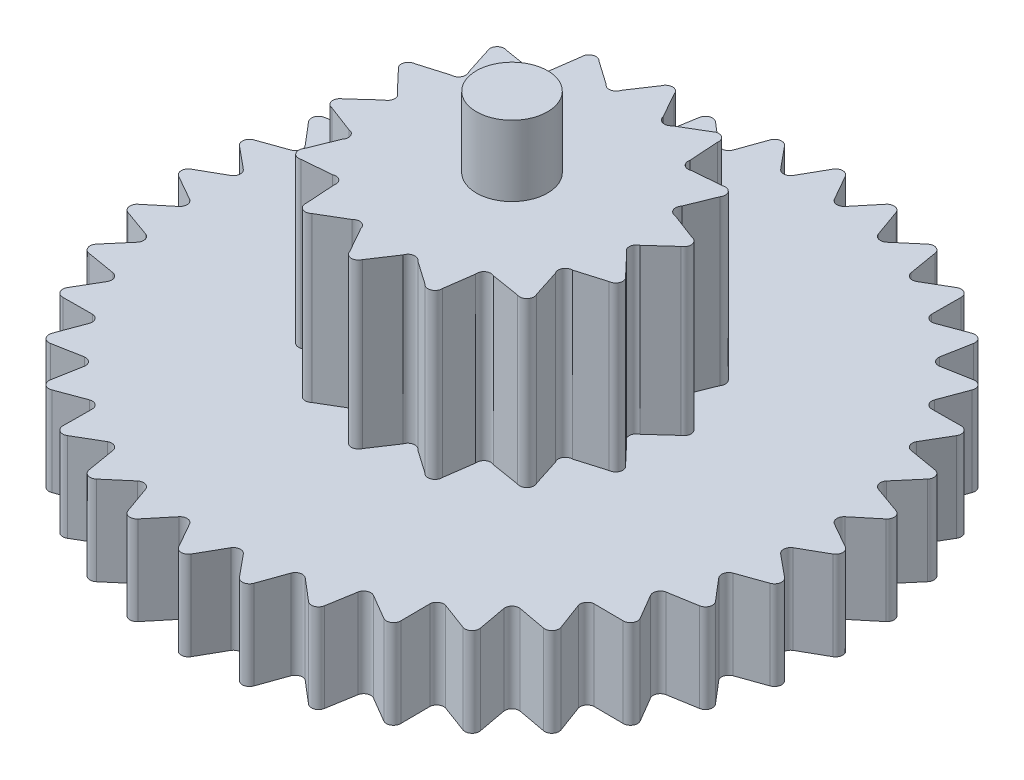
SolidWorks part; units mm, degrees
material "ABS"
ref_plane "Front Plane" through (0, 0, 0) normal (0, 0, 1) x (1, 0, 0)
ref_plane "Top Plane" through (0, 0, 0) normal (0, 1, 0) x (1, 0, 0)
ref_plane "Right Plane" through (0, 0, 0) normal (1, 0, 0) x (0, 0, -1)
sketch "Sketch1" plane through (0, 0, 0) normal (0, 1, 0) x (1, 0, 0)
  line L0 (-8.2272, 4.75) -> (-8.9271, 3.2492) construction
  line L1 (0, 9.5) -> (-1.6497, 9.3557) construction
  line L2 (-1.6497, 9.3557) -> (-3.2492, 8.9271) construction
  line L3 (-3.2492, 8.9271) -> (-4.75, 8.2272) construction
  line L4 (-4.75, 8.2272) -> (-6.1065, 7.2774) construction
  line L5 (-6.1065, 7.2774) -> (-7.2774, 6.1065) construction
  line L6 (-7.2774, 6.1065) -> (-8.2272, 4.75) construction
  line L7 (-8.9271, 3.2492) -> (-9.3557, 1.6497) construction
  line L8 (-9.3557, 1.6497) -> (-9.5, 0) construction
  line L9 (-9.5, 0) -> (-9.3557, -1.6497) construction
  line L10 (-9.3557, -1.6497) -> (-8.9271, -3.2492) construction
  line L11 (-8.9271, -3.2492) -> (-8.2272, -4.75) construction
  line L12 (-8.2272, -4.75) -> (-7.2774, -6.1065) construction
  line L13 (-7.2774, -6.1065) -> (-6.1065, -7.2774) construction
  line L14 (-6.1065, -7.2774) -> (-4.75, -8.2272) construction
  line L15 (-4.75, -8.2272) -> (-3.2492, -8.9271) construction
  line L16 (-3.2492, -8.9271) -> (-1.6497, -9.3557) construction
  line L17 (-1.6497, -9.3557) -> (0, -9.5) construction
  line L18 (0, -9.5) -> (1.6497, -9.3557) construction
  line L19 (1.6497, -9.3557) -> (3.2492, -8.9271) construction
  line L20 (3.2492, -8.9271) -> (4.75, -8.2272) construction
  line L21 (4.75, -8.2272) -> (6.1065, -7.2774) construction
  line L22 (6.1065, -7.2774) -> (7.2774, -6.1065) construction
  line L23 (7.2774, -6.1065) -> (8.2272, -4.75) construction
  line L24 (8.2272, -4.75) -> (8.9271, -3.2492) construction
  line L25 (8.9271, -3.2492) -> (9.3557, -1.6497) construction
  line L26 (9.3557, -1.6497) -> (9.5, 0) construction
  line L27 (9.5, 0) -> (9.3557, 1.6497) construction
  line L28 (9.3557, 1.6497) -> (8.9271, 3.2492) construction
  line L29 (8.9271, 3.2492) -> (8.2272, 4.75) construction
  line L30 (8.2272, 4.75) -> (7.2774, 6.1065) construction
  line L31 (7.2774, 6.1065) -> (6.1065, 7.2774) construction
  line L32 (6.1065, 7.2774) -> (4.75, 8.2272) construction
  line L33 (4.75, 8.2272) -> (3.2492, 8.9271) construction
  line L34 (3.2492, 8.9271) -> (1.6497, 9.3557) construction
  line L35 (1.6497, 9.3557) -> (0, 9.5) construction
  line L36 (0, 9.5) -> (0, 9.2952) construction
  line L37 (0, 9.5) -> (-0.7202, 8.2324) construction
  line L38 (-0.8248, 9.4278) -> (-0.7202, 8.2324) construction
  line L39 (0, 9.5) -> (0.7202, 8.2324) construction
  line L40 (0.7202, 8.2324) -> (0.8248, 9.4278) construction
  line L41 (1.4237, 9.0826) -> (0.901, 8.4508)
  line L42 (0.1751, 9.1918) -> (0.5802, 8.4789)
  line L43 (-0.1751, 9.1918) -> (-0.5802, 8.4789)
  line L44 (1.7686, 9.0218) -> (2.0437, 8.2493)
  line L45 (2.9792, 8.6974) -> (2.3547, 8.166)
  line L46 (3.3083, 8.5776) -> (3.4452, 7.7691)
  line L47 (4.4443, 8.0479) -> (3.737, 7.633)
  line L48 (4.7476, 7.8728) -> (4.7419, 7.0528)
  line L49 (5.7743, 7.1539) -> (5.0057, 6.8681)
  line L50 (6.0425, 6.9288) -> (5.8946, 6.1223)
  line L51 (6.9288, 6.0425) -> (6.1223, 5.8946)
  line L52 (7.1539, 5.7743) -> (6.8681, 5.0057)
  line L53 (7.8728, 4.7476) -> (7.0528, 4.7419)
  line L54 (8.0479, 4.4443) -> (7.633, 3.737)
  line L55 (8.5776, 3.3083) -> (7.7691, 3.4452)
  line L56 (8.6974, 2.9792) -> (8.166, 2.3547)
  line L57 (9.0218, 1.7686) -> (8.2493, 2.0437)
  line L58 (9.0826, 1.4237) -> (8.4508, 0.901)
  line L59 (9.1918, 0.1751) -> (8.4789, 0.5802)
  line L60 (9.1918, -0.1751) -> (8.4789, -0.5802)
  line L61 (9.0826, -1.4237) -> (8.4508, -0.901)
  line L62 (9.0218, -1.7686) -> (8.2493, -2.0437)
  line L63 (8.6974, -2.9792) -> (8.166, -2.3547)
  line L64 (8.5776, -3.3083) -> (7.7691, -3.4452)
  line L65 (8.0479, -4.4443) -> (7.633, -3.737)
  line L66 (7.8728, -4.7476) -> (7.0528, -4.7419)
  line L67 (7.1539, -5.7743) -> (6.8681, -5.0057)
  line L68 (6.9288, -6.0425) -> (6.1223, -5.8946)
  line L69 (6.0425, -6.9288) -> (5.8946, -6.1223)
  line L70 (5.7743, -7.1539) -> (5.0057, -6.8681)
  line L71 (4.7476, -7.8728) -> (4.7419, -7.0528)
  line L72 (4.4443, -8.0479) -> (3.737, -7.633)
  line L73 (3.3083, -8.5776) -> (3.4452, -7.7691)
  line L74 (2.9792, -8.6974) -> (2.3547, -8.166)
  line L75 (1.7686, -9.0218) -> (2.0437, -8.2493)
  line L76 (1.4237, -9.0826) -> (0.901, -8.4508)
  line L77 (0.1751, -9.1918) -> (0.5802, -8.4789)
  line L78 (-0.1751, -9.1918) -> (-0.5802, -8.4789)
  line L79 (-1.4237, -9.0826) -> (-0.901, -8.4508)
  line L80 (-1.7686, -9.0218) -> (-2.0437, -8.2493)
  line L81 (-2.9792, -8.6974) -> (-2.3547, -8.166)
  line L82 (-3.3083, -8.5776) -> (-3.4452, -7.7691)
  line L83 (-4.4443, -8.0479) -> (-3.737, -7.633)
  line L84 (-4.7476, -7.8728) -> (-4.7419, -7.0528)
  line L85 (-5.7743, -7.1539) -> (-5.0057, -6.8681)
  line L86 (-6.0425, -6.9288) -> (-5.8946, -6.1223)
  line L87 (-6.9288, -6.0425) -> (-6.1223, -5.8946)
  line L88 (-7.1539, -5.7743) -> (-6.8681, -5.0057)
  line L89 (-7.8728, -4.7476) -> (-7.0528, -4.7419)
  line L90 (-8.0479, -4.4443) -> (-7.633, -3.737)
  line L91 (-8.5776, -3.3083) -> (-7.7691, -3.4452)
  line L92 (-8.6974, -2.9792) -> (-8.166, -2.3547)
  line L93 (-9.0218, -1.7686) -> (-8.2493, -2.0437)
  line L94 (-9.0826, -1.4237) -> (-8.4508, -0.901)
  line L95 (-9.1918, -0.1751) -> (-8.4789, -0.5802)
  line L96 (-9.1918, 0.1751) -> (-8.4789, 0.5802)
  line L97 (-9.0826, 1.4237) -> (-8.4508, 0.901)
  line L98 (-9.0218, 1.7686) -> (-8.2493, 2.0437)
  line L99 (-8.6974, 2.9792) -> (-8.166, 2.3547)
  line L100 (-8.5776, 3.3083) -> (-7.7691, 3.4452)
  line L101 (-8.0479, 4.4443) -> (-7.633, 3.737)
  line L102 (-7.8728, 4.7476) -> (-7.0528, 4.7419)
  line L103 (-7.1539, 5.7743) -> (-6.8681, 5.0057)
  line L104 (-6.9288, 6.0425) -> (-6.1223, 5.8946)
  line L105 (-6.0425, 6.9288) -> (-5.8946, 6.1223)
  line L106 (-5.7743, 7.1539) -> (-5.0057, 6.8681)
  line L107 (-4.7476, 7.8728) -> (-4.7419, 7.0528)
  line L108 (-4.4443, 8.0479) -> (-3.737, 7.633)
  line L109 (-3.3083, 8.5776) -> (-3.4452, 7.7691)
  line L110 (-2.9792, 8.6974) -> (-2.3547, 8.166)
  line L111 (-1.7686, 9.0218) -> (-2.0437, 8.2493)
  line L112 (-1.4237, 9.0826) -> (-0.901, 8.4508)
  line L113 (0, -9.2952) -> (0, -9.5) construction
  line L114 (0.3636, 4.1956) -> (0.766, 3.4811)
  line L115 (-0.0146, 4.2155) -> (-0.469, 3.5329)
  line L116 (2.1488, 3.6227) -> (2.2013, 2.8044)
  line L117 (1.8167, 3.8048) -> (1.1112, 3.387)
  line L118 (3.5087, 2.332) -> (3.201, 1.572)
  line L119 (3.2885, 2.6402) -> (2.4715, 2.5699)
  line L120 (4.174, 0.5791) -> (3.5669, 0.0279)
  line L121 (4.1092, 0.9523) -> (3.3426, 1.2434)
  line L122 (4.0127, -1.2888) -> (3.2266, -1.5221)
  line L123 (4.1163, -0.9245) -> (3.552, -0.3296)
  line L124 (3.057, -2.9018) -> (2.2475, -2.7709)
  line L125 (3.3084, -2.6185) -> (3.0581, -1.8377)
  line L126 (1.4961, -3.9404) -> (0.8236, -3.4712)
  line L127 (1.8455, -3.7943) -> (1.9587, -2.9821)
  line L128 (-0.3609, -4.1989) -> (-0.7633, -3.4844)
  line L129 (0.0173, -4.2188) -> (0.4717, -3.5362)
  line L130 (-2.1462, -3.6261) -> (-2.1986, -2.8077)
  line L131 (-1.814, -3.8081) -> (-1.1085, -3.3903)
  line L132 (-3.506, -2.3354) -> (-3.1983, -1.5753)
  line L133 (-3.2858, -2.6435) -> (-2.4688, -2.5732)
  line L134 (-4.1713, -0.5824) -> (-3.5642, -0.0312)
  line L135 (-4.1065, -0.9557) -> (-3.3399, -1.2468)
  line L136 (-4.01, 1.2855) -> (-3.2239, 1.5187)
  line L137 (-4.1136, 0.9212) -> (-3.5493, 0.3263)
  line L138 (-3.0543, 2.8985) -> (-2.2448, 2.7676)
  line L139 (-3.3057, 2.6152) -> (-3.0554, 1.8344)
  line L140 (-1.4934, 3.9371) -> (-0.8209, 3.4679)
  line L141 (-1.8428, 3.7909) -> (-1.956, 2.9788)
  circle A0 centre (0, 0) radius 9.5 construction
  arc A1 (-0.1751, 9.1918) -> (0.1751, 9.1918) centre (0, 9.0952) cw
  arc A2 (0.5802, 8.4789) -> (0.7335, 8.3838) centre (0.7509, 8.5831) ccw
  arc A3 (-0.5802, 8.4789) -> (-0.7335, 8.3838) centre (-0.7509, 8.5831) cw
  arc A4 (0.901, 8.4508) -> (0.7335, 8.3838) centre (0.7509, 8.5831) cw
  arc A5 (1.4237, 9.0826) -> (1.7686, 9.0218) centre (1.5794, 8.957) cw
  arc A6 (2.0437, 8.2493) -> (2.1782, 8.1291) centre (2.2299, 8.3223) ccw
  arc A7 (2.3547, 8.166) -> (2.1782, 8.1291) centre (2.2299, 8.3223) cw
  arc A8 (2.9792, 8.6974) -> (3.3083, 8.5776) centre (3.1107, 8.5467) cw
  arc A9 (3.4452, 7.7691) -> (3.5567, 7.6273) centre (3.6412, 7.8086) ccw
  arc A10 (3.737, 7.633) -> (3.5567, 7.6273) centre (3.6412, 7.8086) cw
  arc A11 (4.4443, 8.0479) -> (4.7476, 7.8728) centre (4.5476, 7.8767) cw
  arc A12 (4.7419, 7.0528) -> (4.8271, 6.8939) centre (4.9418, 7.0577) ccw
  arc A13 (5.0057, 6.8681) -> (4.8271, 6.8939) centre (4.9418, 7.0577) cw
  arc A14 (5.7743, 7.1539) -> (6.0425, 6.9288) centre (5.8463, 6.9673) cw
  arc A15 (5.8946, 6.1223) -> (5.9509, 5.9509) centre (6.0923, 6.0923) ccw
  arc A16 (6.1223, 5.8946) -> (5.9509, 5.9509) centre (6.0923, 6.0923) cw
  arc A17 (6.9288, 6.0425) -> (7.1539, 5.7743) centre (6.9673, 5.8463) cw
  arc A18 (6.8681, 5.0057) -> (6.8939, 4.8271) centre (7.0577, 4.9418) ccw
  arc A19 (7.0528, 4.7419) -> (6.8939, 4.8271) centre (7.0577, 4.9418) cw
  arc A20 (7.8728, 4.7476) -> (8.0479, 4.4443) centre (7.8767, 4.5476) cw
  arc A21 (7.633, 3.737) -> (7.6273, 3.5567) centre (7.8086, 3.6412) ccw
  arc A22 (7.7691, 3.4452) -> (7.6273, 3.5567) centre (7.8086, 3.6412) cw
  arc A23 (8.5776, 3.3083) -> (8.6974, 2.9792) centre (8.5467, 3.1107) cw
  arc A24 (8.166, 2.3547) -> (8.1291, 2.1782) centre (8.3223, 2.2299) ccw
  arc A25 (8.2493, 2.0437) -> (8.1291, 2.1782) centre (8.3223, 2.2299) cw
  arc A26 (9.0218, 1.7686) -> (9.0826, 1.4237) centre (8.957, 1.5794) cw
  arc A27 (8.4508, 0.901) -> (8.3838, 0.7335) centre (8.5831, 0.7509) ccw
  arc A28 (8.4789, 0.5802) -> (8.3838, 0.7335) centre (8.5831, 0.7509) cw
  arc A29 (9.1918, 0.1751) -> (9.1918, -0.1751) centre (9.0952, 0) cw
  arc A30 (8.4789, -0.5802) -> (8.3838, -0.7335) centre (8.5831, -0.7509) ccw
  arc A31 (8.4508, -0.901) -> (8.3838, -0.7335) centre (8.5831, -0.7509) cw
  arc A32 (9.0826, -1.4237) -> (9.0218, -1.7686) centre (8.957, -1.5794) cw
  arc A33 (8.2493, -2.0437) -> (8.1291, -2.1782) centre (8.3223, -2.2299) ccw
  arc A34 (8.166, -2.3547) -> (8.1291, -2.1782) centre (8.3223, -2.2299) cw
  arc A35 (8.6974, -2.9792) -> (8.5776, -3.3083) centre (8.5467, -3.1107) cw
  arc A36 (7.7691, -3.4452) -> (7.6273, -3.5567) centre (7.8086, -3.6412) ccw
  arc A37 (7.633, -3.737) -> (7.6273, -3.5567) centre (7.8086, -3.6412) cw
  arc A38 (8.0479, -4.4443) -> (7.8728, -4.7476) centre (7.8767, -4.5476) cw
  arc A39 (7.0528, -4.7419) -> (6.8939, -4.8271) centre (7.0577, -4.9418) ccw
  arc A40 (6.8681, -5.0057) -> (6.8939, -4.8271) centre (7.0577, -4.9418) cw
  arc A41 (7.1539, -5.7743) -> (6.9288, -6.0425) centre (6.9673, -5.8463) cw
  arc A42 (6.1223, -5.8946) -> (5.9509, -5.9509) centre (6.0923, -6.0923) ccw
  arc A43 (5.8946, -6.1223) -> (5.9509, -5.9509) centre (6.0923, -6.0923) cw
  arc A44 (6.0425, -6.9288) -> (5.7743, -7.1539) centre (5.8463, -6.9673) cw
  arc A45 (5.0057, -6.8681) -> (4.8271, -6.8939) centre (4.9418, -7.0577) ccw
  arc A46 (4.7419, -7.0528) -> (4.8271, -6.8939) centre (4.9418, -7.0577) cw
  arc A47 (4.7476, -7.8728) -> (4.4443, -8.0479) centre (4.5476, -7.8767) cw
  arc A48 (3.737, -7.633) -> (3.5567, -7.6273) centre (3.6412, -7.8086) ccw
  arc A49 (3.4452, -7.7691) -> (3.5567, -7.6273) centre (3.6412, -7.8086) cw
  arc A50 (3.3083, -8.5776) -> (2.9792, -8.6974) centre (3.1107, -8.5467) cw
  arc A51 (2.3547, -8.166) -> (2.1782, -8.1291) centre (2.2299, -8.3223) ccw
  arc A52 (2.0437, -8.2493) -> (2.1782, -8.1291) centre (2.2299, -8.3223) cw
  arc A53 (1.7686, -9.0218) -> (1.4237, -9.0826) centre (1.5794, -8.957) cw
  arc A54 (0.901, -8.4508) -> (0.7335, -8.3838) centre (0.7509, -8.5831) ccw
  arc A55 (0.5802, -8.4789) -> (0.7335, -8.3838) centre (0.7509, -8.5831) cw
  arc A56 (0.1751, -9.1918) -> (-0.1751, -9.1918) centre (0, -9.0952) cw
  arc A57 (-0.5802, -8.4789) -> (-0.7335, -8.3838) centre (-0.7509, -8.5831) ccw
  arc A58 (-0.901, -8.4508) -> (-0.7335, -8.3838) centre (-0.7509, -8.5831) cw
  arc A59 (-1.4237, -9.0826) -> (-1.7686, -9.0218) centre (-1.5794, -8.957) cw
  arc A60 (-2.0437, -8.2493) -> (-2.1782, -8.1291) centre (-2.2299, -8.3223) ccw
  arc A61 (-2.3547, -8.166) -> (-2.1782, -8.1291) centre (-2.2299, -8.3223) cw
  arc A62 (-2.9792, -8.6974) -> (-3.3083, -8.5776) centre (-3.1107, -8.5467) cw
  arc A63 (-3.4452, -7.7691) -> (-3.5567, -7.6273) centre (-3.6412, -7.8086) ccw
  arc A64 (-3.737, -7.633) -> (-3.5567, -7.6273) centre (-3.6412, -7.8086) cw
  arc A65 (-4.4443, -8.0479) -> (-4.7476, -7.8728) centre (-4.5476, -7.8767) cw
  arc A66 (-4.7419, -7.0528) -> (-4.8271, -6.8939) centre (-4.9418, -7.0577) ccw
  arc A67 (-5.0057, -6.8681) -> (-4.8271, -6.8939) centre (-4.9418, -7.0577) cw
  arc A68 (-5.7743, -7.1539) -> (-6.0425, -6.9288) centre (-5.8463, -6.9673) cw
  arc A69 (-5.8946, -6.1223) -> (-5.9509, -5.9509) centre (-6.0923, -6.0923) ccw
  arc A70 (-6.1223, -5.8946) -> (-5.9509, -5.9509) centre (-6.0923, -6.0923) cw
  arc A71 (-6.9288, -6.0425) -> (-7.1539, -5.7743) centre (-6.9673, -5.8463) cw
  arc A72 (-6.8681, -5.0057) -> (-6.8939, -4.8271) centre (-7.0577, -4.9418) ccw
  arc A73 (-7.0528, -4.7419) -> (-6.8939, -4.8271) centre (-7.0577, -4.9418) cw
  arc A74 (-7.8728, -4.7476) -> (-8.0479, -4.4443) centre (-7.8767, -4.5476) cw
  arc A75 (-7.633, -3.737) -> (-7.6273, -3.5567) centre (-7.8086, -3.6412) ccw
  arc A76 (-7.7691, -3.4452) -> (-7.6273, -3.5567) centre (-7.8086, -3.6412) cw
  arc A77 (-8.5776, -3.3083) -> (-8.6974, -2.9792) centre (-8.5467, -3.1107) cw
  arc A78 (-8.166, -2.3547) -> (-8.1291, -2.1782) centre (-8.3223, -2.2299) ccw
  arc A79 (-8.2493, -2.0437) -> (-8.1291, -2.1782) centre (-8.3223, -2.2299) cw
  arc A80 (-9.0218, -1.7686) -> (-9.0826, -1.4237) centre (-8.957, -1.5794) cw
  arc A81 (-8.4508, -0.901) -> (-8.3838, -0.7335) centre (-8.5831, -0.7509) ccw
  arc A82 (-8.4789, -0.5802) -> (-8.3838, -0.7335) centre (-8.5831, -0.7509) cw
  arc A83 (-9.1918, -0.1751) -> (-9.1918, 0.1751) centre (-9.0952, 0) cw
  arc A84 (-8.4789, 0.5802) -> (-8.3838, 0.7335) centre (-8.5831, 0.7509) ccw
  arc A85 (-8.4508, 0.901) -> (-8.3838, 0.7335) centre (-8.5831, 0.7509) cw
  arc A86 (-9.0826, 1.4237) -> (-9.0218, 1.7686) centre (-8.957, 1.5794) cw
  arc A87 (-8.2493, 2.0437) -> (-8.1291, 2.1782) centre (-8.3223, 2.2299) ccw
  arc A88 (-8.166, 2.3547) -> (-8.1291, 2.1782) centre (-8.3223, 2.2299) cw
  arc A89 (-8.6974, 2.9792) -> (-8.5776, 3.3083) centre (-8.5467, 3.1107) cw
  arc A90 (-7.7691, 3.4452) -> (-7.6273, 3.5567) centre (-7.8086, 3.6412) ccw
  arc A91 (-7.633, 3.737) -> (-7.6273, 3.5567) centre (-7.8086, 3.6412) cw
  arc A92 (-8.0479, 4.4443) -> (-7.8728, 4.7476) centre (-7.8767, 4.5476) cw
  arc A93 (-7.0528, 4.7419) -> (-6.8939, 4.8271) centre (-7.0577, 4.9418) ccw
  arc A94 (-6.8681, 5.0057) -> (-6.8939, 4.8271) centre (-7.0577, 4.9418) cw
  arc A95 (-7.1539, 5.7743) -> (-6.9288, 6.0425) centre (-6.9673, 5.8463) cw
  arc A96 (-6.1223, 5.8946) -> (-5.9509, 5.9509) centre (-6.0923, 6.0923) ccw
  arc A97 (-5.8946, 6.1223) -> (-5.9509, 5.9509) centre (-6.0923, 6.0923) cw
  arc A98 (-6.0425, 6.9288) -> (-5.7743, 7.1539) centre (-5.8463, 6.9673) cw
  arc A99 (-5.0057, 6.8681) -> (-4.8271, 6.8939) centre (-4.9418, 7.0577) ccw
  arc A100 (-4.7419, 7.0528) -> (-4.8271, 6.8939) centre (-4.9418, 7.0577) cw
  arc A101 (-4.7476, 7.8728) -> (-4.4443, 8.0479) centre (-4.5476, 7.8767) cw
  arc A102 (-3.737, 7.633) -> (-3.5567, 7.6273) centre (-3.6412, 7.8086) ccw
  arc A103 (-3.4452, 7.7691) -> (-3.5567, 7.6273) centre (-3.6412, 7.8086) cw
  arc A104 (-3.3083, 8.5776) -> (-2.9792, 8.6974) centre (-3.1107, 8.5467) cw
  arc A105 (-2.3547, 8.166) -> (-2.1782, 8.1291) centre (-2.2299, 8.3223) ccw
  arc A106 (-2.0437, 8.2493) -> (-2.1782, 8.1291) centre (-2.2299, 8.3223) cw
  arc A107 (-1.7686, 9.0218) -> (-1.4237, 9.0826) centre (-1.5794, 8.957) cw
  arc A108 (-0.901, 8.4508) -> (-0.7335, 8.3838) centre (-0.7509, 8.5831) ccw
  arc A109 (-0.8209, 3.4679) -> (-0.469, 3.5329) centre (-0.6612, 3.5883) ccw
  arc A110 (-0.0146, 4.2155) -> (0.3636, 4.1956) centre (0.1711, 4.1413) cw
  arc A111 (0.766, 3.4811) -> (1.1112, 3.387) centre (0.9621, 3.5203) ccw
  arc A112 (1.8167, 3.8048) -> (2.1488, 3.6227) centre (1.9519, 3.6574) cw
  arc A113 (2.2013, 2.8044) -> (2.4715, 2.5699) centre (2.395, 2.7547) ccw
  arc A114 (3.2885, 2.6402) -> (3.5087, 2.332) centre (3.3463, 2.4487) cw
  arc A115 (3.201, 1.572) -> (3.3426, 1.2434) centre (3.3539, 1.4431) ccw
  arc A116 (4.1092, 0.9523) -> (4.174, 0.5791) centre (4.0783, 0.7547) cw
  arc A117 (3.5669, 0.0279) -> (3.552, -0.3296) centre (3.6488, -0.1546) ccw
  arc A118 (4.1163, -0.9245) -> (4.0127, -1.2888) centre (4.0027, -1.0891) cw
  arc A119 (3.2266, -1.5221) -> (3.0581, -1.8377) centre (3.2212, -1.722) ccw
  arc A120 (3.3084, -2.6185) -> (3.057, -2.9018) centre (3.1346, -2.7175) cw
  arc A121 (2.2475, -2.7709) -> (1.9587, -2.9821) centre (2.1559, -2.9487) ccw
  arc A122 (1.8455, -3.7943) -> (1.4961, -3.9404) centre (1.646, -3.808) cw
  arc A123 (0.8236, -3.4712) -> (0.4717, -3.5362) centre (0.6639, -3.5917) ccw
  arc A124 (0.0173, -4.2188) -> (-0.3609, -4.1989) centre (-0.1684, -4.1447) cw
  arc A125 (-0.7633, -3.4844) -> (-1.1085, -3.3903) centre (-0.9594, -3.5236) ccw
  arc A126 (-1.814, -3.8081) -> (-2.1462, -3.6261) centre (-1.9492, -3.6607) cw
  arc A127 (-2.1986, -2.8077) -> (-2.4688, -2.5732) centre (-2.3923, -2.758) ccw
  arc A128 (-3.2858, -2.6435) -> (-3.506, -2.3354) centre (-3.3436, -2.4521) cw
  arc A129 (-3.1983, -1.5753) -> (-3.3399, -1.2468) centre (-3.3512, -1.4464) ccw
  arc A130 (-4.1065, -0.9557) -> (-4.1713, -0.5824) centre (-4.0756, -0.7581) cw
  arc A131 (-3.5642, -0.0312) -> (-3.5493, 0.3263) centre (-3.6461, 0.1513) ccw
  arc A132 (-4.1136, 0.9212) -> (-4.01, 1.2855) centre (-4, 1.0857) cw
  arc A133 (-3.2239, 1.5187) -> (-3.0554, 1.8344) centre (-3.2185, 1.7187) ccw
  arc A134 (-3.3057, 2.6152) -> (-3.0543, 2.8985) centre (-3.1319, 2.7142) cw
  arc A135 (-2.2448, 2.7676) -> (-1.956, 2.9788) centre (-2.1532, 2.9454) ccw
  arc A136 (-1.8428, 3.7909) -> (-1.4934, 3.9371) centre (-1.6433, 3.8047) cw
  circle A137 centre (0, 0) radius 3.5637 construction
  point P434 (0.0013, -0.0017)
  point P482 (0, 0)
  dimension "D4" = 0.2
  dimension "D5" = 0.4048
  dimension "D7" = 0.2
  dimension "D6" = 0.2
  dimension "D12" = 0.2
  dimension "D13" = 14
  dimension "D14" = 7.1275
  dimension "D11" = 0.2
  dimension "D1" = 19
  dimension "D2" = 0.82
  dimension "D3" = 1.2
  dimension "D8" = 1.6497
  dimension "D10" = 0.82
  dimension "D9" = 36
extrude "Boss-Extrude1" add sketch "Sketch1" along normal blind 2.5
sketch "Sketch2" plane through (0, 0, 0) normal (0, 1, 0) x (1, 0, 0)
  line L0 (-4.01, 1.2855) -> (-3.2239, 1.5187) construction
  line L1 (-3.3057, 2.6152) -> (-3.0554, 1.8344) construction
  line L2 (-3.0543, 2.8985) -> (-2.2448, 2.7676) construction
  line L3 (-1.8428, 3.7909) -> (-1.956, 2.9788) construction
  line L4 (-1.4934, 3.9371) -> (-0.8209, 3.4679) construction
  line L5 (-0.0146, 4.2155) -> (-0.469, 3.5329) construction
  line L6 (0.3636, 4.1956) -> (0.766, 3.4811) construction
  line L7 (1.8167, 3.8048) -> (1.1112, 3.387) construction
  line L8 (2.1488, 3.6227) -> (2.2013, 2.8044) construction
  line L9 (3.2885, 2.6402) -> (2.4715, 2.5699) construction
  line L10 (3.5087, 2.332) -> (3.201, 1.572) construction
  line L11 (4.1092, 0.9523) -> (3.3426, 1.2434) construction
  line L12 (4.174, 0.5791) -> (3.5669, 0.0279) construction
  line L13 (4.1163, -0.9245) -> (3.552, -0.3296) construction
  line L14 (4.0127, -1.2888) -> (3.2266, -1.5221) construction
  line L15 (3.3084, -2.6185) -> (3.0581, -1.8377) construction
  line L16 (3.057, -2.9018) -> (2.2475, -2.7709) construction
  line L17 (1.8455, -3.7943) -> (1.9587, -2.9821) construction
  line L18 (1.4961, -3.9404) -> (0.8236, -3.4712) construction
  line L19 (-0.3609, -4.1989) -> (-0.7633, -3.4844) construction
  line L20 (-1.814, -3.8081) -> (-1.1085, -3.3903) construction
  line L21 (-2.1462, -3.6261) -> (-2.1986, -2.8077) construction
  line L22 (-3.2858, -2.6435) -> (-2.4688, -2.5732) construction
  line L23 (-3.506, -2.3354) -> (-3.1983, -1.5753) construction
  line L24 (-4.1065, -0.9557) -> (-3.3399, -1.2468) construction
  line L25 (-4.1713, -0.5824) -> (-3.5642, -0.0312) construction
  line L26 (-4.1136, 0.9212) -> (-3.5493, 0.3263) construction
  line L27 (0.0173, -4.2188) -> (0.4717, -3.5362) construction
  line L28 (-4.01, 1.2855) -> (-3.2239, 1.5187)
  line L29 (-3.3057, 2.6152) -> (-3.0554, 1.8344)
  line L30 (-3.0543, 2.8985) -> (-2.2448, 2.7676)
  line L31 (-1.8428, 3.7909) -> (-1.956, 2.9788)
  line L32 (-1.4934, 3.9371) -> (-0.8209, 3.4679)
  line L33 (-0.0146, 4.2155) -> (-0.469, 3.5329)
  line L34 (0.3636, 4.1956) -> (0.766, 3.4811)
  line L35 (1.8167, 3.8048) -> (1.1112, 3.387)
  line L36 (2.1488, 3.6227) -> (2.2013, 2.8044)
  line L37 (3.2885, 2.6402) -> (2.4715, 2.5699)
  line L38 (3.5087, 2.332) -> (3.201, 1.572)
  line L39 (4.1092, 0.9523) -> (3.3426, 1.2434)
  line L40 (4.174, 0.5791) -> (3.5669, 0.0279)
  line L41 (4.1163, -0.9245) -> (3.552, -0.3296)
  line L42 (4.0127, -1.2888) -> (3.2266, -1.5221)
  line L43 (3.3084, -2.6185) -> (3.0581, -1.8377)
  line L44 (3.057, -2.9018) -> (2.2475, -2.7709)
  line L45 (1.8455, -3.7943) -> (1.9587, -2.9821)
  line L46 (1.4961, -3.9404) -> (0.8236, -3.4712)
  line L47 (-0.3609, -4.1989) -> (-0.7633, -3.4844)
  line L48 (-1.814, -3.8081) -> (-1.1085, -3.3903)
  line L49 (-2.1462, -3.6261) -> (-2.1986, -2.8077)
  line L50 (-3.2858, -2.6435) -> (-2.4688, -2.5732)
  line L51 (-3.506, -2.3354) -> (-3.1983, -1.5753)
  line L52 (-4.1065, -0.9557) -> (-3.3399, -1.2468)
  line L53 (-4.1713, -0.5824) -> (-3.5642, -0.0312)
  line L54 (-4.1136, 0.9212) -> (-3.5493, 0.3263)
  line L55 (0.0173, -4.2188) -> (0.4717, -3.5362)
  arc A0 (-3.2239, 1.5187) -> (-3.0554, 1.8344) centre (-3.2185, 1.7187) ccw construction
  arc A1 (-3.0543, 2.8985) -> (-3.3057, 2.6152) centre (-3.1319, 2.7142) ccw construction
  arc A2 (-2.2448, 2.7676) -> (-1.956, 2.9788) centre (-2.1532, 2.9454) ccw construction
  arc A3 (-1.4934, 3.9371) -> (-1.8428, 3.7909) centre (-1.6433, 3.8047) ccw construction
  arc A4 (-0.8209, 3.4679) -> (-0.469, 3.5329) centre (-0.6612, 3.5883) ccw construction
  arc A5 (0.3636, 4.1956) -> (-0.0146, 4.2155) centre (0.1711, 4.1413) ccw construction
  arc A6 (0.766, 3.4811) -> (1.1112, 3.387) centre (0.9621, 3.5203) ccw construction
  arc A7 (2.1488, 3.6227) -> (1.8167, 3.8048) centre (1.9519, 3.6574) ccw construction
  arc A8 (2.2013, 2.8044) -> (2.4715, 2.5699) centre (2.395, 2.7547) ccw construction
  arc A9 (3.5087, 2.332) -> (3.2885, 2.6402) centre (3.3463, 2.4487) ccw construction
  arc A10 (3.201, 1.572) -> (3.3426, 1.2434) centre (3.3539, 1.4431) ccw construction
  arc A11 (4.174, 0.5791) -> (4.1092, 0.9523) centre (4.0783, 0.7547) ccw construction
  arc A12 (3.5669, 0.0279) -> (3.552, -0.3296) centre (3.6488, -0.1546) ccw construction
  arc A13 (4.0127, -1.2888) -> (4.1163, -0.9245) centre (4.0027, -1.0891) ccw construction
  arc A14 (3.2266, -1.5221) -> (3.0581, -1.8377) centre (3.2212, -1.722) ccw construction
  arc A15 (3.057, -2.9018) -> (3.3084, -2.6185) centre (3.1346, -2.7175) ccw construction
  arc A16 (2.2475, -2.7709) -> (1.9587, -2.9821) centre (2.1559, -2.9487) ccw construction
  arc A17 (1.4961, -3.9404) -> (1.8455, -3.7943) centre (1.646, -3.808) ccw construction
  arc A18 (0.8236, -3.4712) -> (0.4717, -3.5362) centre (0.6639, -3.5917) ccw construction
  arc A19 (-0.3609, -4.1989) -> (0.0173, -4.2188) centre (-0.1684, -4.1447) ccw construction
  arc A20 (-0.7633, -3.4844) -> (-1.1085, -3.3903) centre (-0.9594, -3.5236) ccw construction
  arc A21 (-2.1462, -3.6261) -> (-1.814, -3.8081) centre (-1.9492, -3.6607) ccw construction
  arc A22 (-2.1986, -2.8077) -> (-2.4688, -2.5732) centre (-2.3923, -2.758) ccw construction
  arc A23 (-3.506, -2.3354) -> (-3.2858, -2.6435) centre (-3.3436, -2.4521) ccw construction
  arc A24 (-3.1983, -1.5753) -> (-3.3399, -1.2468) centre (-3.3512, -1.4464) ccw construction
  arc A25 (-4.1713, -0.5824) -> (-4.1065, -0.9557) centre (-4.0756, -0.7581) ccw construction
  arc A26 (-3.5642, -0.0312) -> (-3.5493, 0.3263) centre (-3.6461, 0.1513) ccw construction
  arc A27 (-4.01, 1.2855) -> (-4.1136, 0.9212) centre (-4, 1.0857) ccw construction
  arc A28 (-3.2239, 1.5187) -> (-3.0554, 1.8344) centre (-3.2185, 1.7187) ccw
  arc A29 (-3.0543, 2.8985) -> (-3.3057, 2.6152) centre (-3.1319, 2.7142) ccw
  arc A30 (-2.2448, 2.7676) -> (-1.956, 2.9788) centre (-2.1532, 2.9454) ccw
  arc A31 (-1.4934, 3.9371) -> (-1.8428, 3.7909) centre (-1.6433, 3.8047) ccw
  arc A32 (-0.8209, 3.4679) -> (-0.469, 3.5329) centre (-0.6612, 3.5883) ccw
  arc A33 (0.3636, 4.1956) -> (-0.0146, 4.2155) centre (0.1711, 4.1413) ccw
  arc A34 (0.766, 3.4811) -> (1.1112, 3.387) centre (0.9621, 3.5203) ccw
  arc A35 (2.1488, 3.6227) -> (1.8167, 3.8048) centre (1.9519, 3.6574) ccw
  arc A36 (2.2013, 2.8044) -> (2.4715, 2.5699) centre (2.395, 2.7547) ccw
  arc A37 (3.5087, 2.332) -> (3.2885, 2.6402) centre (3.3463, 2.4487) ccw
  arc A38 (3.201, 1.572) -> (3.3426, 1.2434) centre (3.3539, 1.4431) ccw
  arc A39 (4.174, 0.5791) -> (4.1092, 0.9523) centre (4.0783, 0.7547) ccw
  circle A40 centre (0, 0) radius 1
  arc A41 (3.5669, 0.0279) -> (3.552, -0.3296) centre (3.6488, -0.1546) ccw
  arc A42 (4.0127, -1.2888) -> (4.1163, -0.9245) centre (4.0027, -1.0891) ccw
  arc A43 (3.2266, -1.5221) -> (3.0581, -1.8377) centre (3.2212, -1.722) ccw
  arc A44 (3.057, -2.9018) -> (3.3084, -2.6185) centre (3.1346, -2.7175) ccw
  arc A45 (2.2475, -2.7709) -> (1.9587, -2.9821) centre (2.1559, -2.9487) ccw
  arc A46 (1.4961, -3.9404) -> (1.8455, -3.7943) centre (1.646, -3.808) ccw
  arc A47 (0.8236, -3.4712) -> (0.4717, -3.5362) centre (0.6639, -3.5917) ccw
  arc A48 (-0.3609, -4.1989) -> (0.0173, -4.2188) centre (-0.1684, -4.1447) ccw
  arc A49 (-0.7633, -3.4844) -> (-1.1085, -3.3903) centre (-0.9594, -3.5236) ccw
  arc A50 (-2.1462, -3.6261) -> (-1.814, -3.8081) centre (-1.9492, -3.6607) ccw
  arc A51 (-2.1986, -2.8077) -> (-2.4688, -2.5732) centre (-2.3923, -2.758) ccw
  arc A52 (-3.506, -2.3354) -> (-3.2858, -2.6435) centre (-3.3436, -2.4521) ccw
  arc A53 (-3.1983, -1.5753) -> (-3.3399, -1.2468) centre (-3.3512, -1.4464) ccw
  arc A54 (-4.1713, -0.5824) -> (-4.1065, -0.9557) centre (-4.0756, -0.7581) ccw
  arc A55 (-3.5642, -0.0312) -> (-3.5493, 0.3263) centre (-3.6461, 0.1513) ccw
  arc A56 (-4.01, 1.2855) -> (-4.1136, 0.9212) centre (-4, 1.0857) ccw
  point P0 (3.5669, 0.0279)
  dimension "D1" = 2
extrude "Boss-Extrude2" add sketch "Sketch2" along normal blind 7.1
sketch "Sketch3" plane through (0, 0, 0) normal (0, 1, 0) x (1, 0, 0)
  circle A1 centre (0, 0) radius 1 construction
  circle A2 centre (0, 0) radius 1
extrude "Boss-Extrude3" add sketch "Sketch3" along normal blind 9.08 and the other way blind 2.6
fillet "Fillet1" radius 1 1 edges at (0, -2.6, 1)
sketch "Axis" plane through (0, 0, 0) normal (0, 0, 1) x (1, 0, 0)
  line L0 (0, 0) -> (0, 9.08) construction
  line L1 (1, 9.08) -> (-1, 9.08) construction
